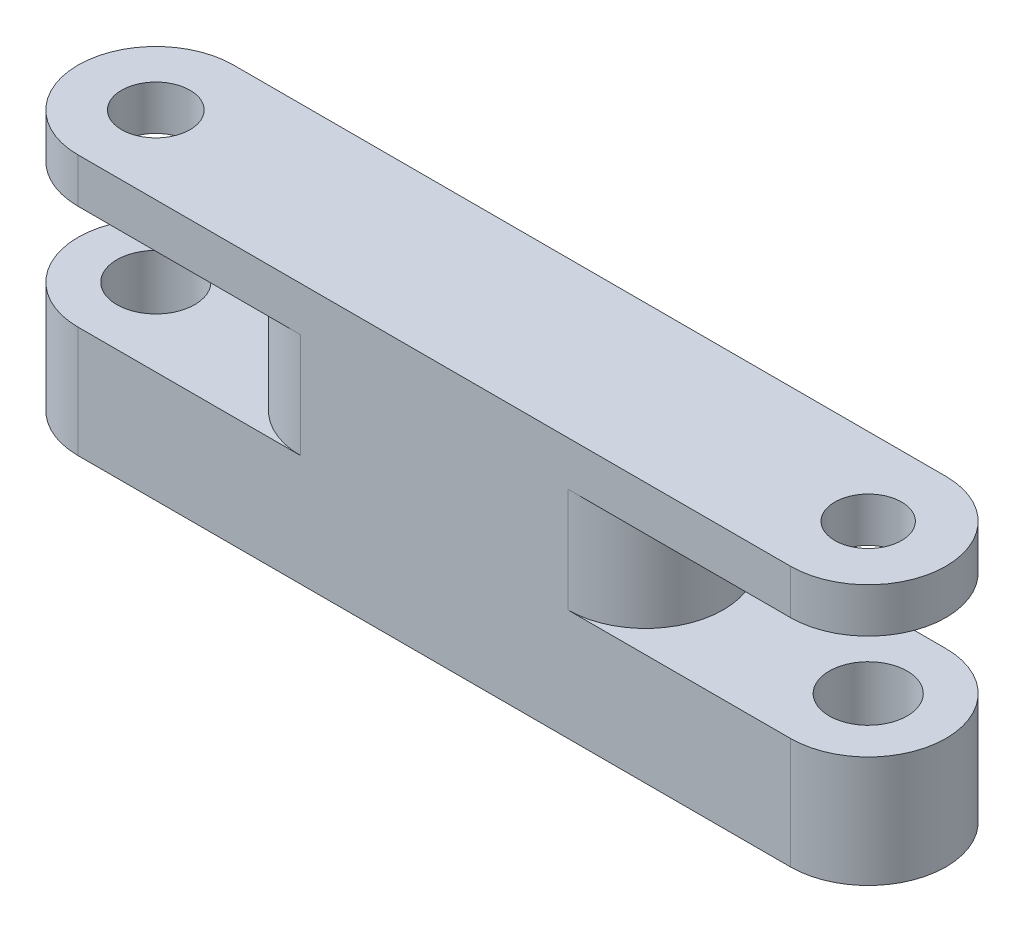
SolidWorks part; units mm, degrees
ref_plane "Alzado" through (0, 0, 0) normal (0, 0, 1) x (1, 0, 0)
ref_plane "Planta" through (0, 0, 0) normal (0, 1, 0) x (1, 0, 0)
ref_plane "Vista lateral" through (0, 0, 0) normal (1, 0, 0) x (0, 0, -1)
sketch "Croquis1" plane through (0, 0, 0) normal (0, 1, 0) x (1, 0, 0)
  line L1 (4.5686, 0) -> (36.5686, 0)
  line L3 (4.5686, 6.9872) -> (36.5686, 6.9872)
  circle A0 centre (4.5686, 3.4936) radius 3.4936
  circle A1 centre (36.5686, 3.4936) radius 3.4936
  circle A2 centre (4.5686, 3.4936) radius 1.75
  circle A3 centre (36.5686, 3.4936) radius 1.75
  dimension "D1" = 3.5
  dimension "D2" = 3.5
  dimension "D3" = 32
extrude "Saliente-Extruir1" add sketch "Croquis1" along normal blind 5 contours A1 L3 A0 L1 | A1 A3 | A2
sketch "Croquis2" plane through (0, 5, 0) normal (0, 1, 0) x (1, 0, 0)
  line L0 (4.5686, 6.9872) -> (36.5686, 6.9872) construction
  line L1 (14.5686, 6.9872) -> (26.5686, 6.9872)
  line L2 (14.5686, 6.9872) -> (14.5686, 0)
  line L3 (14.5686, 0) -> (26.5686, 0)
  line L4 (26.5686, 6.9872) -> (26.5686, 0)
  line L5 (4.5686, 0) -> (36.5686, 0) construction
  line L6 (20.5686, 6.9872) -> (20.5686, 0) construction
  circle A0 centre (26.5686, 3.4936) radius 3.4936
  circle A1 centre (14.5686, 3.4936) radius 3.4936
  line M5 (4.5686, 0) -> (36.5686, 0)
  line M7 (36.5686, 6.9872) -> (4.5686, 6.9872)
  dimension "D1" = 12
  dimension "D2" = 6
extrude "Saliente-Extruir2" add sketch "Croquis2" along normal blind 4.7 contours L6 L3 A0 M7 | L4 A0 | L4 A0 | L2 A1 | L2 A1 | L6 L1 A1 M5
sketch "Croquis3" plane through (0, 9.7, 0) normal (0, 1, 0) x (1, 0, 0)
  line L0 (4.5686, 6.9872) -> (36.5686, 6.9872)
  line L1 (4.5686, 0) -> (36.5686, 0)
  circle A0 centre (4.5686, 3.4936) radius 1.5373
  arc A1 (4.5686, 6.9872) -> (4.5686, 0) centre (4.5686, 3.4936) ccw
  arc A2 (36.5686, 0) -> (36.5686, 6.9872) centre (36.5686, 3.4936) ccw
  circle A3 centre (36.5686, 3.4936) radius 1.5
  line M1 (26.5686, 6.9872) -> (14.5686, 6.9872)
  arc M2 (14.5686, 6.9872) -> (14.5686, 0) centre (14.5686, 3.4936) ccw
  line M3 (14.5686, 0) -> (26.5686, 0)
  arc M4 (26.5686, 0) -> (26.5686, 6.9872) centre (26.5686, 3.4936) ccw
extrude "Saliente-Extruir3" add sketch "Croquis3" along normal blind 2 contours A1 L1 L0 M2 | M4 M1 M2 M3 | A1 A0 | A2 A3 | A2 L0 L1 M4
